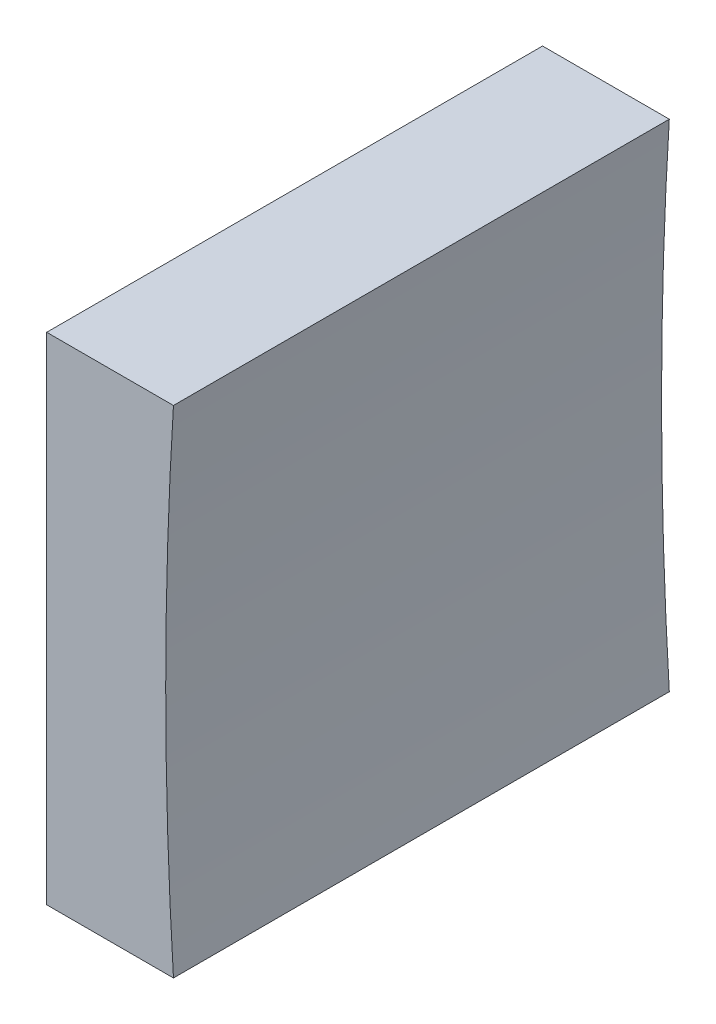
SolidWorks part; units mm, degrees
ref_plane "前视基准面" through (0, 0, 0) normal (0, 0, 1) x (1, 0, 0)
ref_plane "上视基准面" through (0, 0, 0) normal (0, 1, 0) x (1, 0, 0)
ref_plane "右视基准面" through (0, 0, 0) normal (1, 0, 0) x (0, 0, -1)
sketch "草图1" plane through (0, 0, 0) normal (0, 0, 1) x (1, 0, 0)
  line L0 (278.655, 66.8579) -> (298.183, 66.8579) construction
  line L1 (284.7071, 66.8579) -> (284.7071, 79.3579)
  line L2 (284.7071, 79.3579) -> (291.0981, 79.3579)
  line L3 (291.0981, 54.3579) -> (284.7071, 54.3579)
  line L4 (284.7071, 54.3579) -> (284.7071, 66.8579)
  arc A0 (291.0981, 79.3579) -> (291.0981, 54.3579) centre (490.7071, 66.8579) ccw
  dimension "D1" = 200
extrude "凸台-拉伸1" add sketch "草图1" along normal blind 25
